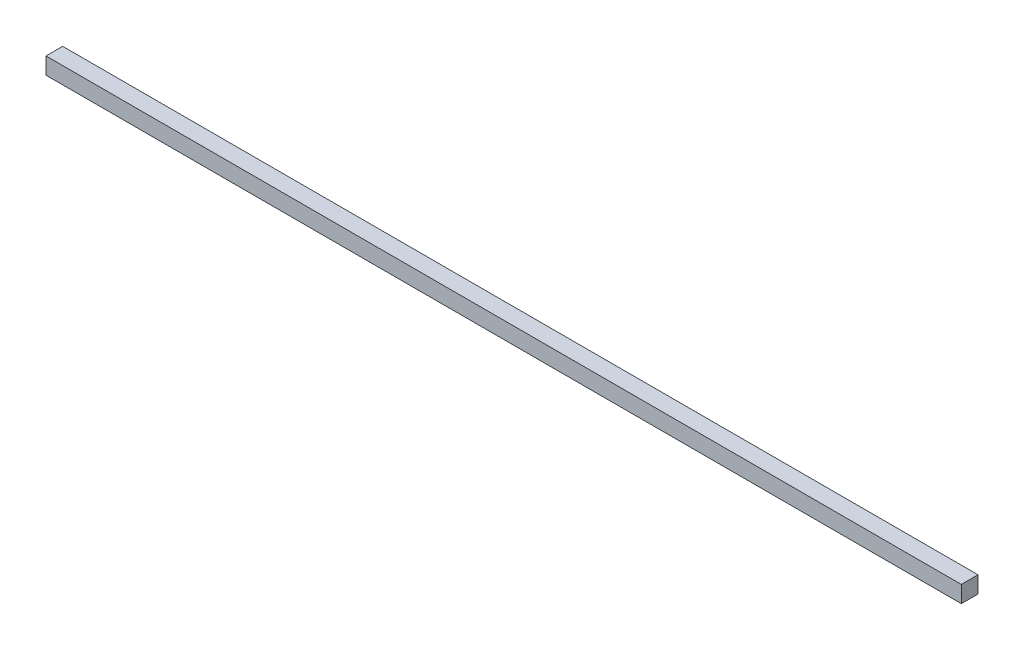
SolidWorks part; units mm, degrees
ref_plane "Front Plane" through (0, 0, 0) normal (0, 0, 1) x (1, 0, 0)
ref_plane "Top Plane" through (0, 0, 0) normal (0, 1, 0) x (1, 0, 0)
ref_plane "Right Plane" through (0, 0, 0) normal (1, 0, 0) x (0, 0, -1)
sketch "Sketch1" plane through (0, 0, 0) normal (0, 1, 0) x (1, 0, 0)
  line L0 (-274.265, 5) -> (274.265, -5) construction
  line L1 (-274.265, 5) -> (274.265, 5)
  line L2 (-274.265, 5) -> (-274.265, -5)
  line L3 (-274.265, -5) -> (274.265, -5)
  line L4 (274.265, 5) -> (274.265, -5)
  dimension "D1" = 548.53
  dimension "D2" = 10
extrude "Boss-Extrude1" add sketch "Sketch1" along normal blind 10
